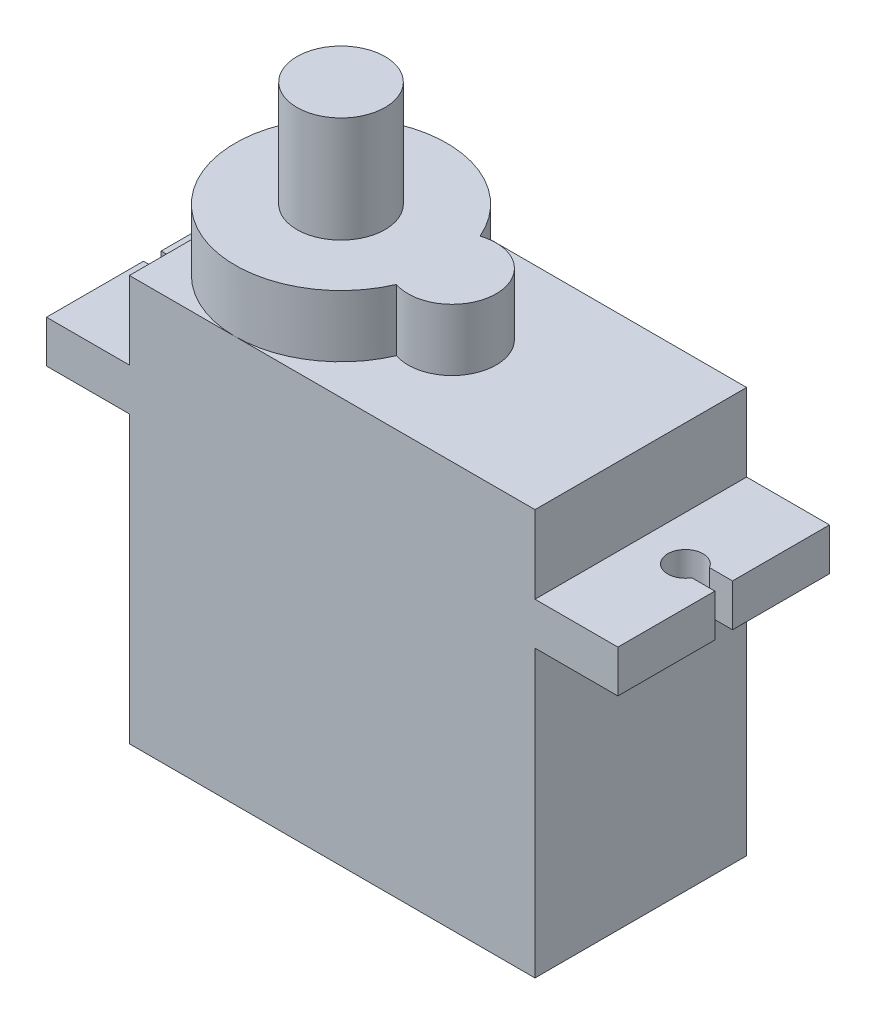
SolidWorks part; units mm, degrees
ref_plane "Front Plane" through (0, 0, 0) normal (0, 0, 1) x (1, 0, 0)
ref_plane "Top Plane" through (0, 0, 0) normal (0, 1, 0) x (1, 0, 0)
ref_plane "Right Plane" through (0, 0, 0) normal (1, 0, 0) x (0, 0, -1)
sketch "Sketch2" plane through (0, 0, 0) normal (0, 1, 0) x (1, 0, 0)
  line L1 (-11.5, -6) -> (11.5, -6)
  line L2 (-11.5, -6) -> (-11.5, 6)
  line L3 (-11.5, 6) -> (11.5, 6)
  line L4 (11.5, -6) -> (11.5, 6)
  line L5 (-11.5, -6) -> (11.5, 6) construction
  line L6 (-11.5, 6) -> (11.5, -6) construction
  point P0 (0, 0)
  dimension "D1" = 12
  dimension "D2" = 23
extrude "Boss-Extrude1" add sketch "Sketch2" against normal blind 23
sketch "Sketch3" plane through (0, 0, 0) normal (0, 1, 0) x (1, 0, 0)
  line L0 (11.5, 6) -> (-11.5, 6) construction
  line L1 (-16.2, -6) -> (16.2, -6)
  line L2 (-16.2, -6) -> (-16.2, 6)
  line L3 (-16.2, 6) -> (16.2, 6)
  line L4 (16.2, -6) -> (16.2, 6)
  line L5 (-16.2, -6) -> (16.2, 6) construction
  line L6 (-16.2, 6) -> (16.2, -6) construction
  line L8 (-15.5843, 0.5) -> (-16.2, 0.5)
  line L9 (-15.5843, 0.5) -> (-15.5843, -0.5)
  line L10 (-15.5843, -0.5) -> (-16.2, -0.5)
  line L11 (-16.2, 0.5) -> (-16.2, -0.5)
  line L12 (16.2, 0.5) -> (14.8944, 0.5)
  line L13 (16.2, 0.5) -> (16.2, -0.5)
  line L14 (16.2, -0.5) -> (14.8944, -0.5)
  line L15 (14.8944, 0.5) -> (14.8944, -0.5)
  circle A0 centre (-14.7183, 0) radius 1
  circle A1 centre (14.0284, 0) radius 1
  point P0 (0, 0)
  line M15 (11.5, -6) -> (11.5, 6)
  line M17 (-11.5, 6) -> (-11.5, -6)
  dimension "D2" = 2
  dimension "D1" = 32.4
  dimension "D3" = 1
  dimension "D4" = 1
  dimension "D5" = 28.7466
  dimension "D6" = 12
extrude "Boss-Extrude2" add sketch "Sketch3" against normal blind 2.4 from offset 4.4 contours A0 L10 L2 L1 L3 L8 M17 | A1 L12 L4 L3 L1 L14 M15 offset against normal yes
sketch "Sketch4" plane through (0, 0, 0) normal (0, 1, 0) x (1, 0, 0)
  line L0 (-11.5, 6) -> (-11.5, -6) construction
  line L1 (11.5, 6) -> (-11.5, 6) construction
  line L2 (3.3, 0) -> (-11.5, 0) construction
  circle A0 centre (-5.5, 0) radius 6
  circle A1 centre (0.8, 0) radius 2.5
  dimension "D1" = 14.8
  dimension "D2" = 5
extrude "Boss-Extrude3" add sketch "Sketch4" along normal blind 3.5 contours L2 A1 A0 | A1 L2 A0 | A1 L2 A0 | L2 A1 A0 | L2 A0 A1 | A0 L2 A1
sketch "Sketch5" plane through (0, 3.5, 0) normal (0, 1, 0) x (1, 0, 0)
  line L0 (-3.255, -0.15) -> (-3.4372, 0)
  line L1 (-3.4372, 0) -> (-3.255, 0.15)
  line L2 (-3.295, -0.4479) -> (-3.4556, -0.2749)
  line L3 (-3.4556, -0.2749) -> (-3.255, -0.1506)
  line L4 (-3.3744, -0.7378) -> (-3.5105, -0.545)
  line L5 (-3.5105, -0.545) -> (-3.2951, -0.4484)
  line L6 (-3.4917, -1.0145) -> (-3.6009, -0.8053)
  line L7 (-3.6009, -0.8053) -> (-3.3746, -0.7383)
  line L8 (-3.6448, -1.2731) -> (-3.7252, -1.0512)
  line L9 (-3.7252, -1.0512) -> (-3.492, -1.015)
  line L10 (-3.8311, -1.5091) -> (-3.8811, -1.2784)
  line L11 (-3.8811, -1.2784) -> (-3.6452, -1.2736)
  line L12 (-4.0471, -1.718) -> (-4.0659, -1.4828)
  line L13 (-4.0659, -1.4828) -> (-3.8315, -1.5095)
  line L14 (-4.2891, -1.8964) -> (-4.2764, -1.6607)
  line L15 (-4.2764, -1.6607) -> (-4.0476, -1.7184)
  line L16 (-4.5526, -2.0408) -> (-4.5086, -1.809)
  line L17 (-4.5086, -1.809) -> (-4.2896, -1.8967)
  line L18 (-4.8331, -2.1489) -> (-4.7586, -1.925)
  line L19 (-4.7586, -1.925) -> (-4.5532, -2.0411)
  line L20 (-5.1255, -2.2186) -> (-5.0218, -2.0066)
  line L21 (-5.0218, -2.0066) -> (-4.8337, -2.1491)
  line L22 (-5.4245, -2.2487) -> (-5.2935, -2.0525)
  line L23 (-5.2935, -2.0525) -> (-5.126, -2.2187)
  line L24 (-5.7249, -2.2387) -> (-5.5689, -2.0617)
  line L25 (-5.5689, -2.0617) -> (-5.4251, -2.2488)
  line L26 (-6.0213, -2.1888) -> (-5.8431, -2.0341)
  line L27 (-5.8431, -2.0341) -> (-5.7255, -2.2387)
  line L28 (-6.3084, -2.0998) -> (-6.1112, -1.9702)
  line L29 (-6.1112, -1.9702) -> (-6.0219, -2.1886)
  line L30 (-6.5811, -1.9733) -> (-6.3683, -1.8712)
  line L31 (-6.3683, -1.8712) -> (-6.3089, -2.0996)
  line L32 (-6.8344, -1.8116) -> (-6.61, -1.7387)
  line L33 (-6.61, -1.7387) -> (-6.5816, -1.973)
  line L34 (-7.064, -1.6176) -> (-6.8318, -1.5753)
  line L35 (-6.8318, -1.5753) -> (-6.8349, -1.8112)
  line L36 (-7.2656, -1.3947) -> (-7.0299, -1.3837)
  line L37 (-7.0299, -1.3837) -> (-7.0644, -1.6172)
  line L38 (-7.4358, -1.1469) -> (-7.2007, -1.1674)
  line L39 (-7.2007, -1.1674) -> (-7.266, -1.3942)
  line L40 (-7.5714, -0.8786) -> (-7.3411, -0.9304)
  line L41 (-7.3411, -0.9304) -> (-7.436, -1.1464)
  line L42 (-7.67, -0.5947) -> (-7.4487, -0.6767)
  line L43 (-7.4487, -0.6767) -> (-7.5716, -0.8781)
  line L44 (-7.7299, -0.3002) -> (-7.5215, -0.4109)
  line L45 (-7.5215, -0.4109) -> (-7.6701, -0.5942)
  line L46 (-7.75, -0.0003) -> (-7.5582, -0.1378)
  line L47 (-7.5582, -0.1378) -> (-7.73, -0.2996)
  line L48 (-7.73, 0.2996) -> (-7.5582, 0.1378)
  line L49 (-7.5582, 0.1378) -> (-7.75, 0.0003)
  line L50 (-7.6701, 0.5942) -> (-7.5215, 0.4109)
  line L51 (-7.5215, 0.4109) -> (-7.7299, 0.3002)
  line L52 (-7.5716, 0.8781) -> (-7.4487, 0.6767)
  line L53 (-7.4487, 0.6767) -> (-7.67, 0.5947)
  line L54 (-7.436, 1.1464) -> (-7.3411, 0.9304)
  line L55 (-7.3411, 0.9304) -> (-7.5714, 0.8786)
  line L56 (-7.266, 1.3942) -> (-7.2007, 1.1674)
  line L57 (-7.2007, 1.1674) -> (-7.4358, 1.1469)
  line L58 (-7.0644, 1.6172) -> (-7.0299, 1.3837)
  line L59 (-7.0299, 1.3837) -> (-7.2656, 1.3947)
  line L60 (-6.8349, 1.8112) -> (-6.8318, 1.5753)
  line L61 (-6.8318, 1.5753) -> (-7.064, 1.6176)
  line L62 (-6.5816, 1.973) -> (-6.61, 1.7387)
  line L63 (-6.61, 1.7387) -> (-6.8344, 1.8116)
  line L64 (-6.3089, 2.0996) -> (-6.3683, 1.8712)
  line L65 (-6.3683, 1.8712) -> (-6.5811, 1.9733)
  line L66 (-6.0219, 2.1886) -> (-6.1112, 1.9702)
  line L67 (-6.1112, 1.9702) -> (-6.3084, 2.0998)
  line L68 (-5.7255, 2.2387) -> (-5.8431, 2.0341)
  line L69 (-5.8431, 2.0341) -> (-6.0213, 2.1888)
  line L70 (-5.4251, 2.2488) -> (-5.5689, 2.0617)
  line L71 (-5.5689, 2.0617) -> (-5.7249, 2.2387)
  line L72 (-5.126, 2.2187) -> (-5.2935, 2.0525)
  line L73 (-5.2935, 2.0525) -> (-5.4245, 2.2487)
  line L74 (-4.8337, 2.1491) -> (-5.0218, 2.0066)
  line L75 (-5.0218, 2.0066) -> (-5.1255, 2.2186)
  line L76 (-4.5532, 2.0411) -> (-4.7586, 1.925)
  line L77 (-4.7586, 1.925) -> (-4.8331, 2.1489)
  line L78 (-4.2896, 1.8967) -> (-4.5086, 1.809)
  line L79 (-4.5086, 1.809) -> (-4.5526, 2.0408)
  line L80 (-4.0476, 1.7184) -> (-4.2764, 1.6607)
  line L81 (-4.2764, 1.6607) -> (-4.2891, 1.8964)
  line L82 (-3.8315, 1.5095) -> (-4.0659, 1.4828)
  line L83 (-4.0659, 1.4828) -> (-4.0471, 1.718)
  line L84 (-3.6452, 1.2736) -> (-3.8811, 1.2784)
  line L85 (-3.8811, 1.2784) -> (-3.8311, 1.5091)
  line L86 (-3.492, 1.015) -> (-3.7252, 1.0512)
  line L87 (-3.7252, 1.0512) -> (-3.6448, 1.2731)
  line L88 (-3.3746, 0.7383) -> (-3.6009, 0.8053)
  line L89 (-3.6009, 0.8053) -> (-3.4917, 1.0145)
  line L90 (-3.2951, 0.4484) -> (-3.5105, 0.545)
  line L91 (-3.5105, 0.545) -> (-3.3744, 0.7378)
  line L92 (-3.255, 0.1506) -> (-3.4556, 0.2749)
  line L93 (-3.4556, 0.2749) -> (-3.295, 0.4479)
  circle A0 centre (-5.5, 0) radius 2.25
  point P146 (-5.5, 0)
  dimension "D1" = 4.5
  dimension "D2" = 0.15
  dimension "D3" = 47
extrude "Boss-Extrude4" add sketch "Sketch5" along normal blind 3 contours L25 A0 L22 L23 L20 L21 L18 L19 L16 L17 L14 L15 L12 L13 L10 L11 L8 L9 L6 L7 L4 L5 L2 L3 L0 L1 L92 L93 L90 L91 L88 L89 L86 L87 L84
sketch "Sketch6" plane through (-11.5, 0, 0) normal (-1, 0, 0) x (0, 0, 1)
  line L0 (-6, -23) -> (6, -23) construction
  line L1 (-1.5, -17) -> (1.5, -17)
  line L2 (-1.5, -17) -> (-1.5, -18)
  line L3 (-1.5, -18) -> (1.5, -18)
  line L4 (1.5, -17) -> (1.5, -18)
  point P7 (0, -17)
  dimension "D1" = 5
  dimension "D2" = 3
  dimension "D3" = 1
extrude "Boss-Extrude5" add sketch "Sketch6" along normal blind 3
sketch "Sketch7" plane through (0, 6.5, 0) normal (0, 1, 0) x (1, 0, 0)
  circle A0 centre (-5.5, 0) radius 2.5
  dimension "D1" = 5
extrude "Boss-Extrude6" add sketch "Sketch7" against normal mid plane 6
